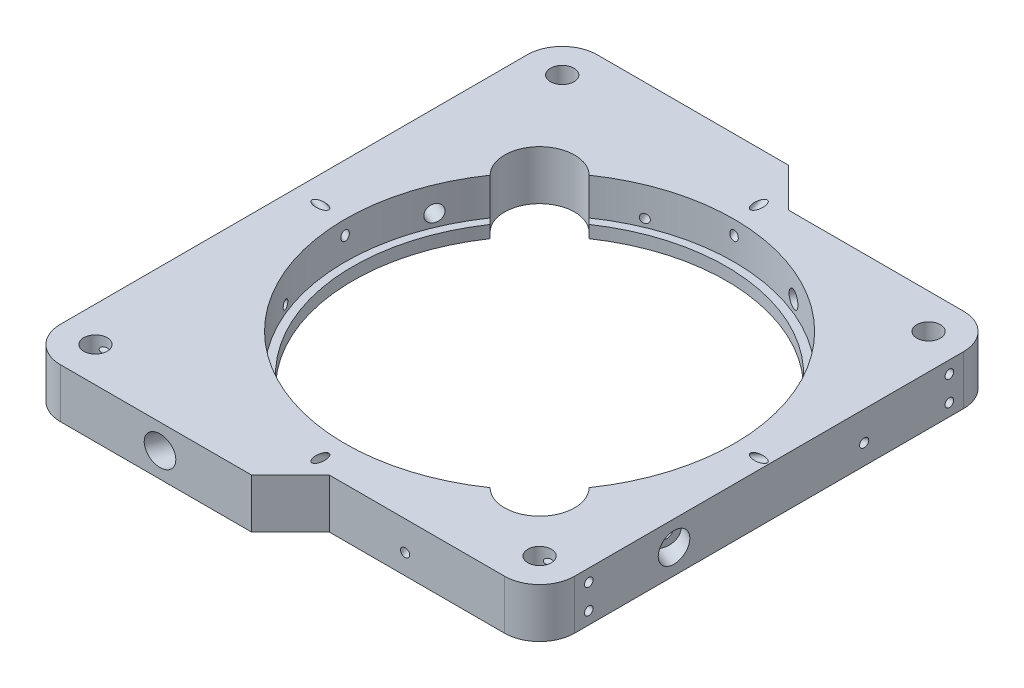
SolidWorks part; units mm, degrees
ref_plane "Front Plane" through (0, 0, 0) normal (0, 0, 1) x (1, 0, 0)
ref_plane "Top Plane" through (0, 0, 0) normal (0, 1, 0) x (1, 0, 0)
ref_plane "Right Plane" through (0, 0, 0) normal (1, 0, 0) x (0, 0, -1)
sketch "Sketch1" plane through (0, 0, 0) normal (0, 1, 0) x (1, 0, 0)
  line L0 (-50, 50) -> (-50, 60) construction
  line L1 (-50, 50) -> (50, 50) construction
  line L2 (5, 59) -> (50, 59)
  line L3 (-59, 59) -> (50, 59) construction
  line L4 (50, 50) -> (50, -50) construction
  line L5 (5, -59) -> (50, -59)
  line L6 (50, -50) -> (-50, -50) construction
  line L7 (-50, -50) -> (-50, 50) construction
  line L8 (59, 50) -> (59, -50)
  line L9 (-59, 59) -> (59, -59) construction
  line L10 (-59, -59) -> (59, 59) construction
  line L11 (-50, 60) -> (-54.1825, 60) construction
  line L12 (5, 59) -> (-5, 69)
  line L13 (-54.1825, -60) -> (-50, -60) construction
  line L14 (-50, -60) -> (-50, -50) construction
  line L15 (-5, 69) -> (-54.1825, 69)
  line L16 (-63.1825, 60) -> (-63.1825, -60)
  line L17 (-54.1825, -69) -> (-5, -69)
  line L18 (-5, -69) -> (5, -59)
  line L19 (-59, 59) -> (-59, -59) construction
  line L20 (-59, -59) -> (50, -59) construction
  circle A0 centre (50, 50) radius 3.025
  circle A1 centre (50, -50) radius 3.025
  arc A2 (-54.1825, 69) -> (-63.1825, 60) centre (-54.1825, 60) ccw
  arc A3 (-63.1825, -60) -> (-54.1825, -69) centre (-54.1825, -60) ccw
  arc A5 (50, -59) -> (59, -50) centre (50, -50) ccw
  arc A6 (50, 59) -> (59, 50) centre (50, 50) cw
  circle A8 centre (-54.1825, 60) radius 3.025
  circle A9 centre (-54.1825, -60) radius 3.025
  point P8 (50, 0)
  point P9 (0, 50)
  point P10 (0, 0)
  point P11 (-50, 0)
  point P12 (0, -50)
  point P18 (0, -64)
  point P27 (0, 64)
  dimension "D1" = 6.05
  dimension "D4" = 9
  dimension "D7" = 9
  dimension "D2" = 100
  dimension "D3" = 9
  dimension "D5" = 4.1825
  dimension "D6" = 10
extrude "Boss-Extrude1" add sketch "Sketch1" along normal blind 12.7
sketch "Sketch2" plane through (59, 0, 0) normal (1, 0, 0) x (0, 0, -1)
  line L0 (46.34, 12.7) -> (46.975, 12.7) construction
  line L1 (46.34, 12.7) -> (46.34, 9.525) construction
  line L2 (-50, 12.7) -> (50, 12.7) construction
  line L3 (46.34, 9.525) -> (46.34, 3.175) construction
  line L4 (46.34, 3.175) -> (46.34, 0) construction
  line L5 (-50, 0) -> (50, 0) construction
  line L6 (-46.34, 12.7) -> (-46.34, 9.525) construction
  line L7 (-46.34, 9.525) -> (-46.34, 3.175) construction
  line L8 (-46.34, 3.175) -> (-46.34, 0) construction
  line L9 (-46.975, 12.7) -> (-46.34, 12.7) construction
  circle A0 centre (-46.34, 9.525) radius 1.095
  circle A1 centre (-46.34, 3.175) radius 1.095
  circle A2 centre (46.34, 9.525) radius 1.095
  circle A3 centre (46.34, 3.175) radius 1.095
  dimension "D1" = 2.19
  dimension "D2" = 3.175
  dimension "D3" = 0.635
extrude "Cut-Extrude1" cut sketch "Sketch2" against normal blind 15
sketch "Sketch4" plane through (0, 0, 0) normal (0, 0, 1) x (1, 0, 0)
  line L0 (0, 0) -> (0, 12.7)
  line L1 (5, 12.7) -> (50, 12.7) construction
  line L2 (0, 12.7) -> (50, 12.7)
  line L3 (50, 12.7) -> (50, 3.175)
  line L4 (50, 3.175) -> (48, 3.175)
  line L5 (48, 3.175) -> (48, 0)
  line L6 (5, 0) -> (50, 0) construction
  line L7 (48, 0) -> (0, 0)
  line L8 (-5, 12.7) -> (5, 12.7) construction
  dimension "D1" = 2
  dimension "D2" = 50
  dimension "D3" = 9.525
revolve "Cut-Revolve1" cut sketch "Sketch4" angle 360 about L0
ref_axis "Axis1" through (0, 13.335, 0) along (0, -1, 0)
ref_plane "Plane1" through (0, 0, 0) normal (-0.3827, 0, 0.9239) x (0.9239, 0, 0.3827)
sketch "Sketch5" plane through (0, 0, 0) normal (-0.3827, 0, 0.9239) x (0.9239, 0, 0.3827)
  line L0 (0, 12.7) -> (0, 0) construction
  line L1 (0, 13.335) -> (0, -0.635) construction
  line L2 (27.1977, 12.7) -> (68.7723, 12.7) construction
  line L5 (27.1977, 0) -> (68.7723, 0) construction
  circle A0 centre (0, 6.35) radius 2.1
  point P10 (0, 6.35)
  dimension "D2" = 4.2
extrude "Cut-Extrude2" cut sketch "Sketch5" against normal through all
ref_plane "Plane2" through (0, 0, 0) normal (-0.9239, 0, 0.3827) x (0.3827, 0, 0.9239)
sketch "Sketch6" plane through (0, 0, 0) normal (-0.9239, 0, 0.3827) x (0.3827, 0, 0.9239)
  line L0 (-79.6117, 12.7) -> (31.2539, 12.7) construction
  line L1 (0, 12.7) -> (0, 3.175) construction
  line L3 (50, 12.7) -> (-50, 12.7) construction
  line L4 (50, 3.175) -> (-50, 3.175) construction
  line L5 (0, 13.335) -> (0, -0.635) construction
  circle A0 centre (0, 5.175) radius 1.095
  dimension "D1" = 2.19
  dimension "D2" = 2
extrude "Cut-Extrude3" cut sketch "Sketch6" against normal through all
ref_plane "Plane3" through (0, 0, 50) normal (0, 0, -1) x (-1, 0, 0)
ref_plane "Plane4" through (0, 25.5477, 44.25) normal (0, -0.5, -0.866) x (-1, 0, 0)
sketch "Sketch7" plane through (0, 25.5477, 44.25) normal (0, -0.5, -0.866) x (-1, 0, 0)
  line L0 (0, -14.0015) -> (0, -17.1765) construction
  line L1 (0, 11.5484) -> (0, -0.5499) construction
  circle A0 centre (0, -17.1765) radius 1.095
  ellipse E1 centre (0, 10.9985) end of major axis (-50, 10.9985) minor radius 25 construction
  dimension "D1" = 2.19
  dimension "D2" = 3.175
extrude "Cut-Extrude4" cut sketch "Sketch7" against normal up to surface and the other way up to surface up to face at (50, 12.7, 0) other way up to face at (45.7757, 5.4266, -20.1144)
pattern_circular "CirPattern1" count 4 over 360 about axis through (0, 13.335, 0) along (0, -1, 0) of "Cut-Extrude2", "Cut-Extrude3", "Cut-Extrude4"
sketch "Sketch8" plane through (0, 12.7, 0) normal (0, 1, 0) x (1, 0, 0)
  line L0 (-41.1418, 28.4139) -> (-39.7031, 26.9752)
  line L1 (-39.7031, 26.9752) -> (-26.9752, 39.7031)
  line L2 (-26.9752, 39.7031) -> (-28.4139, 41.1418)
  line L3 (0, 0) -> (-34.7779, 34.7779) construction
  line L4 (-34.7779, 34.7779) -> (-59, 59) construction
  arc A0 (-41.1418, 28.4139) -> (-28.4139, 41.1418) centre (-34.7779, 34.7779) cw
  circle A1 centre (0, 0) radius 50 construction
  circle A2 centre (0, 0) radius 48 construction
  point P3 (-33.3392, 33.3392)
  dimension "D2" = 9
  dimension "D1" = 18
extrude "Cut-Extrude5" cut sketch "Sketch8" against normal through all
pattern_circular "CirPattern2" count 2 over 360 about axis through (0, 0, 0) along (0, 1, 0) of "Cut-Extrude5"
sketch "Sketch9" plane through (0, 0, 0) normal (-0.3827, 0, 0.9239) x (0.9239, 0, 0.3827)
  line L0 (0, 13.335) -> (0, -0.635) construction
  circle A0 centre (0, 6.35) radius 3.75
  circle A1 centre (0, 6.35) radius 2.1 construction
  dimension "D1" = 7.5
extrude "Cut-Extrude6" cut sketch "Sketch9" along normal blind 5 and the other way through all from offset 63.3333
pattern_circular "CirPattern6" count 4 over 360 about axis through (0, 0, 0) along (0, 1, 0) of "Cut-Extrude6"
sketch "Sketch10" plane through (-63.1825, 0, 0) normal (-1, 0, 0) x (0, 0, 1)
  line L0 (56.34, 12.7) -> (56.34, 9.525) construction
  line L1 (-60, 12.7) -> (60, 12.7) construction
  line L3 (-56.34, 12.7) -> (-56.34, 9.525) construction
  line L4 (-56.34, 9.525) -> (-56.34, 3.175) construction
  line L5 (-56.34, 3.175) -> (-56.34, 0) construction
  line L6 (-50, 0) -> (-59, 0) construction
  line L7 (56.34, 9.525) -> (56.34, 3.175) construction
  line L8 (56.34, 3.175) -> (56.34, 0) construction
  line L9 (59, 0) -> (50, 0) construction
  circle A0 centre (56.34, 9.525) radius 1.095
  circle A1 centre (56.34, 3.175) radius 1.095
  circle A2 centre (-56.34, 9.525) radius 1.095
  circle A3 centre (-56.34, 3.175) radius 1.095
  dimension "D1" = 2.19
  dimension "D2" = 0.635
  dimension "D3" = 0.635
  dimension "D4" = 3.175
extrude "Cut-Extrude7" cut sketch "Sketch10" against normal blind 16
